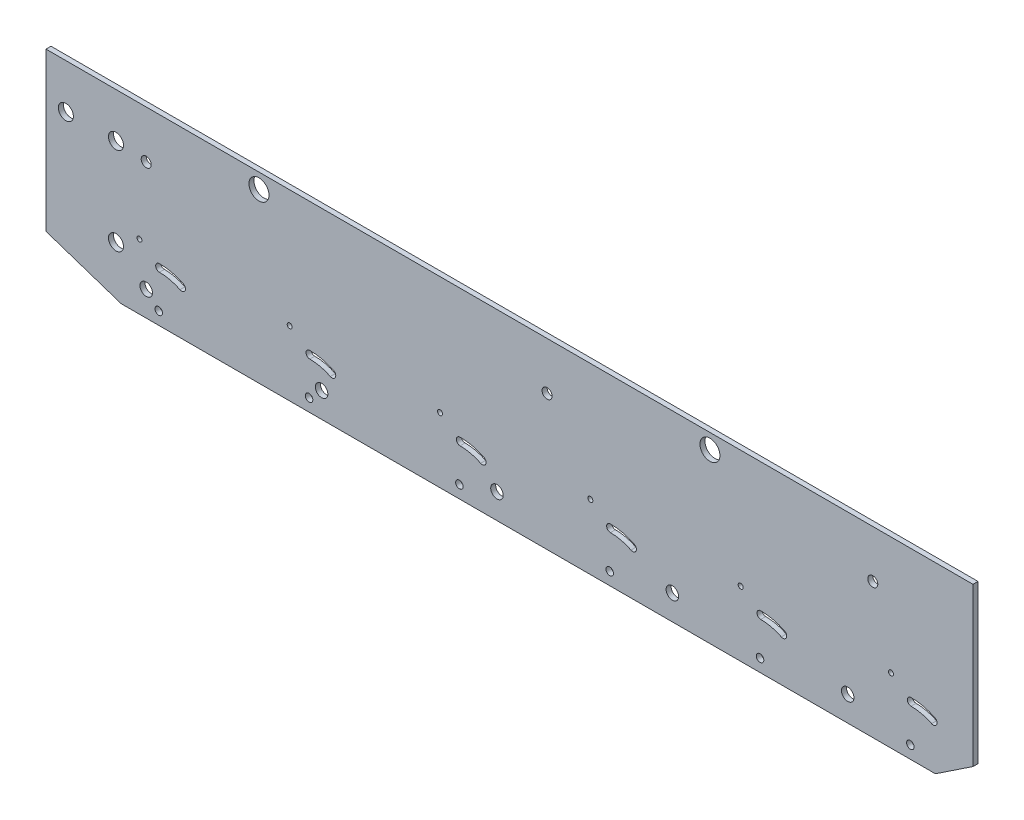
SolidWorks part; units mm, degrees
ref_plane "前视基准面" through (0, 0, 0) normal (0, 0, 1) x (1, 0, 0)
ref_plane "上视基准面" through (0, 0, 0) normal (0, 1, 0) x (1, 0, 0)
ref_plane "右视基准面" through (0, 0, 0) normal (1, 0, 0) x (0, 0, -1)
sketch "草图1" plane through (0, 0, 0) normal (0, 0, 1) x (1, 0, 0)
  line L0 (-162.5, 0) -> (162.5, 0)
  line L1 (-192.5, 10) -> (-192.5, 60)
  line L2 (-192.5, 60) -> (177.5, 60)
  line L3 (177.5, 60) -> (177.5, 10)
  line L4 (-192.5, 10) -> (-162.5, 0)
  line L5 (162.5, 0) -> (177.5, 10)
  point P4 (0, 0)
  dimension "D1" = 50
  dimension "D2" = 370
  dimension "D3" = 10
  dimension "D4" = 30
  dimension "D5" = 10
  dimension "D6" = 15
extrude "凸台-拉伸1" add sketch "草图1" along normal blind 2 contours L2 L3 L5 L0 L4 L1
sketch "草图2" plane through (0, 0, 2) normal (0, 0, 1) x (1, 0, 0)
  line L0 (-162.5, 0) -> (162.5, 0) construction
  circle A0 centre (-147.5, 5) radius 1.5
  dimension "D1" = 3
  dimension "D2" = 5
  dimension "D3" = 15
extrude "切除-拉伸1" cut sketch "草图2" against normal blind 2
pattern_linear "阵列(线性)1" count 6 spacing 60 along (1, 0, 0) of "切除-拉伸1"
sketch "草图3" plane through (0, 0, 2) normal (0, 0, 1) x (1, 0, 0)
  line L0 (-162.5, 0) -> (162.5, 0) construction
  line L1 (-192.5, 10) -> (-192.5, 60) construction
  circle A0 centre (-152.5, 10) radius 2.5
  dimension "D1" = 5
  dimension "D2" = 10
  dimension "D3" = 40
extrude "切除-拉伸2" cut sketch "草图3" against normal blind 2
pattern_linear "阵列(线性)2" count 5 spacing 70 along (1, 0, 0) of "切除-拉伸2"
sketch "草图4" plane through (0, 0, 2) normal (0, 0, 1) x (1, 0, 0)
  line L0 (-192.5, 10) -> (-192.5, 60) construction
  line L1 (-192.5, 60) -> (177.5, 60) construction
  line L2 (177.5, 60) -> (177.5, 10) construction
  circle A0 centre (-152.5, 54) radius 2
  circle A1 centre (7.5, 54) radius 2
  circle A2 centre (137.5, 54) radius 2
  dimension "D1" = 4
  dimension "D2" = 4
  dimension "D3" = 4
  dimension "D4" = 40
  dimension "D5" = 6
  dimension "D6" = 200
  dimension "D7" = 6
  dimension "D8" = 40
  dimension "D9" = 6
extrude "切除-拉伸3" cut sketch "草图4" against normal blind 2
sketch "草图6" plane through (0, 0, 2) normal (0, 0, 1) x (1, 0, 0)
  line L0 (-192.5, 10) -> (-192.5, 60) construction
  line L2 (-192.5, 60) -> (177.5, 60) construction
  circle A0 centre (-184.57, 55.21) radius 3
  circle A1 centre (-164.57, 55.21) radius 3
  circle A2 centre (-164.57, 20.21) radius 3
  dimension "D1" = 6
  dimension "D2" = 7.93
  dimension "D3" = 35
  dimension "D4" = 20
  dimension "D5" = 4.79
extrude "切除-拉伸5" cut sketch "草图6" against normal up to next
sketch "草图7" plane through (0, 0, 2) normal (0, 0, 1) x (1, 0, 0)
  line L0 (-162.5, 0) -> (162.5, 0) construction
  line L1 (-192.5, 10) -> (-192.5, 60) construction
  arc A0 (-147.22, 21.5) -> (-147.22, 18.5) centre (-147.22, 20) ccw
  arc A1 (-147.22, 18.5) -> (-139.004, 16.5755) centre (-147.22, 0) cw
  arc A2 (-147.22, 21.5) -> (-137.6716, 19.2634) centre (-147.22, 0) cw
  arc A3 (-139.004, 16.5755) -> (-137.6716, 19.2634) centre (-138.3378, 17.9194) ccw
  dimension "D3" = 3
  dimension "D4" = 1.5
  dimension "D1" = 20
  dimension "D2" = 45.28
extrude "切除-拉伸6" cut sketch "草图7" against normal up to next (2 mm away) contours A2 A3 A1 A0
pattern_linear "阵列(线性)3" count 6 spacing 60 along (1, 0, 0) of "切除-拉伸6"
sketch "草图8" plane through (0, 0, 2) normal (0, 0, 1) x (1, 0, 0)
  line L0 (-162.5, 0) -> (162.5, 0) construction
  circle A0 centre (-155.22, 26) radius 1
  arc A1 (-147.22, 21.5) -> (-147.22, 18.5) centre (-147.22, 20) ccw construction
  dimension "D1" = 2
  dimension "D3" = 8
  dimension "D2" = 26
extrude "切除-拉伸7" cut sketch "草图8" against normal up to next (2 mm away)
pattern_linear "阵列(线性)4" count 6 spacing 60 along (1, 0, 0) of "切除-拉伸7"
sketch "草图9" plane through (0, 0, 0) normal (0, 0, 1) x (1, 0, 0)
  line L1 (-192.5, 60) -> (177.5, 60)
  line L2 (-192.5, 60) -> (-192.5, 73)
  line L3 (-192.5, 73) -> (177.5, 73)
  line L4 (177.5, 60) -> (177.5, 73)
  dimension "D1" = 13
  dimension "D2" = 370
extrude "凸台-拉伸2" add sketch "草图9" along normal blind 2
sketch "草图10" plane through (0, 0, 2) normal (0, 0, 1) x (1, 0, 0)
  line L0 (-192.5, 10) -> (-192.5, 73) construction
  line L1 (177.5, 73) -> (-192.5, 73) construction
  circle A0 centre (-107.5, 67) radius 4
  circle A1 centre (72.5, 67) radius 4
  dimension "D1" = 8
  dimension "D2" = 85
  dimension "D3" = 265
  dimension "D4" = 6
extrude "切除-拉伸8" cut sketch "草图10" against normal blind 2
